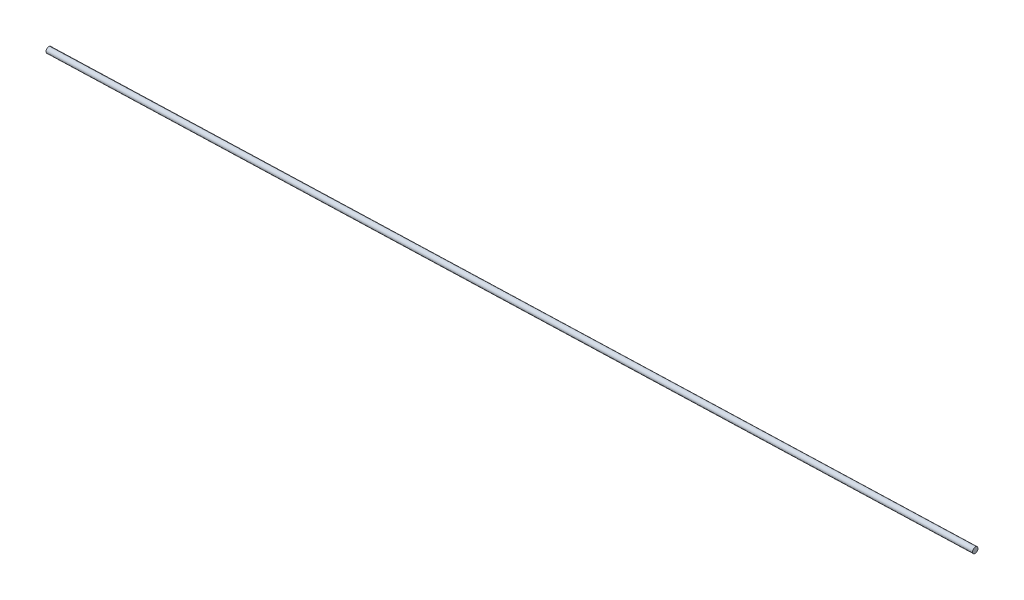
SolidWorks part; units mm, degrees
material "Hexcel AS4C (3000 Filaments)"
ref_plane "Front Plane" through (0, 0, 0) normal (0, 0, 1) x (1, 0, 0)
ref_plane "Top Plane" through (0, 0, 0) normal (0, 1, 0) x (1, 0, 0)
ref_plane "Right Plane" through (0, 0, 0) normal (1, 0, 0) x (0, 0, -1)
sketch "Sketch2" plane through (-1604.7743, 0.5056, 54.2363) normal (-0.9994, 0.0003, 0.0338) x (0.0338, -0.0005, 0.9994)
  circle A1 centre (2.159, 0) radius 3.175
extrude "Boss-Extrude1" add sketch "Sketch2" along normal blind 1016
